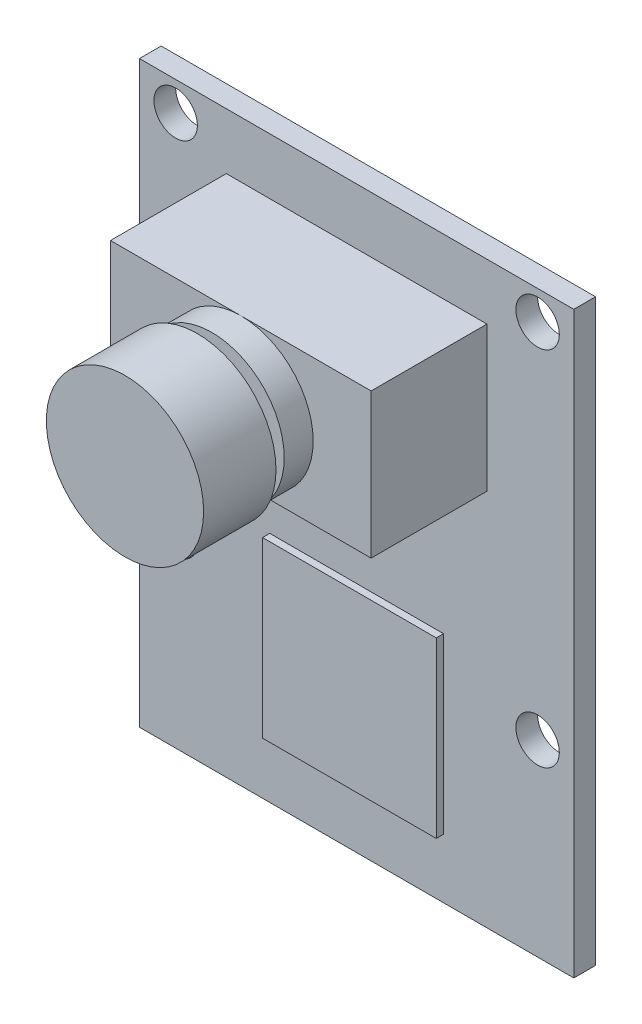
SolidWorks part; units mm, degrees
ref_plane "前视基准面" through (0, 0, 0) normal (0, 0, 1) x (1, 0, 0)
ref_plane "上视基准面" through (0, 0, 0) normal (0, 1, 0) x (1, 0, 0)
ref_plane "右视基准面" through (0, 0, 0) normal (1, 0, 0) x (0, 0, -1)
sketch "草图1" plane through (0, 0, 0) normal (0, 0, 1) x (1, 0, 0)
  line L1 (15, -20) -> (-15, -20)
  line L2 (15, -20) -> (15, 20)
  line L3 (15, 20) -> (-15, 20)
  line L4 (-15, -20) -> (-15, 20)
  line L5 (15, -20) -> (-15, 20) construction
  line L6 (15, 20) -> (-15, -20) construction
  point P0 (0, 0)
extrude "凸台-拉伸1" add sketch "草图1" along normal blind 1.5
sketch "草图2" plane through (0, 0, 1.5) normal (0, 0, 1) x (1, 0, 0)
  line L0 (0, 20) -> (0, -20) construction
  line L1 (15, 20) -> (-15, 20) construction
  line L2 (-15, -20) -> (15, -20) construction
  line L4 (12.5, -7.0105) -> (-12.5, -7.0105) construction
  line L5 (12.5, -7.0105) -> (12.5, 17.9895) construction
  line L6 (12.5, 17.9895) -> (-12.5, 17.9895) construction
  line L7 (-12.5, -7.0105) -> (-12.5, 17.9895) construction
  line L8 (12.5, -7.0105) -> (-12.5, 17.9895) construction
  line L9 (12.5, 17.9895) -> (-12.5, -7.0105) construction
  circle A0 centre (-12.5, 17.9895) radius 1.5
  circle A1 centre (12.5, 17.9895) radius 1.5
  circle A2 centre (-12.5, -7.0105) radius 1.5
  circle A3 centre (12.5, -7.0105) radius 1.5
  point P6 (0, 5.4895)
extrude "切除-拉伸1" cut sketch "草图2" against normal through all
sketch "草图3" plane through (0, 0, 1.5) normal (0, 0, 1) x (1, 0, 0)
  line L0 (0, 20) -> (0, -20) construction
  line L1 (15, 20) -> (-15, 20) construction
  line L2 (-15, -20) -> (15, -20) construction
  line L4 (9, 6.1168) -> (-9, 6.1168)
  line L5 (9, 6.1168) -> (9, 16.1168)
  line L6 (9, 16.1168) -> (-9, 16.1168)
  line L7 (-9, 6.1168) -> (-9, 16.1168)
  line L8 (9, 6.1168) -> (-9, 16.1168) construction
  line L9 (9, 16.1168) -> (-9, 6.1168) construction
  point P6 (0, 11.1168)
  point P11 (0, 11.1168)
extrude "凸台-拉伸2" add sketch "草图3" along normal blind 8
sketch "草图4" plane through (0, 0, 9.5) normal (0, 0, 1) x (1, 0, 0)
  line L0 (-9, 11.1168) -> (9, 11.1168) construction
  line L1 (-9, 16.1168) -> (-9, 6.1168) construction
  line L2 (9, 6.1168) -> (9, 16.1168) construction
  circle A0 centre (0, 11.1168) radius 5
extrude "凸台-拉伸3" add sketch "草图4" along normal blind 2
sketch "草图5" plane through (0, 0, 11.5) normal (0, 0, 1) x (1, 0, 0)
  circle A0 centre (0, 11.1168) radius 3.7826
extrude "凸台-拉伸4" add sketch "草图5" along normal blind 1
sketch "草图6" plane through (0, 0, 12.5) normal (0, 0, 1) x (1, 0, 0)
  circle A0 centre (0, 11.1168) radius 5.4316
extrude "凸台-拉伸5" add sketch "草图6" along normal blind 5
sketch "草图7" plane through (0, 0, 1.5) normal (0, 0, 1) x (1, 0, 0)
  line L0 (0, 20) -> (0, -20) construction
  line L1 (15, 20) -> (-15, 20) construction
  line L2 (-15, -20) -> (15, -20) construction
  line L4 (6, -15.9031) -> (-6, -15.9031)
  line L5 (6, -15.9031) -> (6, -3.9031)
  line L6 (6, -3.9031) -> (-6, -3.9031)
  line L7 (-6, -15.9031) -> (-6, -3.9031)
  line L8 (6, -15.9031) -> (-6, -3.9031) construction
  line L9 (6, -3.9031) -> (-6, -15.9031) construction
  point P6 (0, -9.9031)
extrude "凸台-拉伸6" add sketch "草图7" along normal blind 0.5
